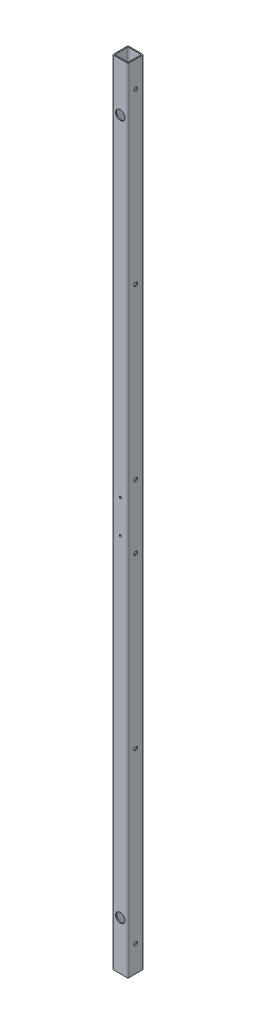
SolidWorks part; units mm, degrees
ref_plane "Front Plane" through (0, 0, 0) normal (0, 0, 1) x (1, 0, 0)
ref_plane "Top Plane" through (0, 0, 0) normal (0, 1, 0) x (1, 0, 0)
ref_plane "Right Plane" through (0, 0, 0) normal (1, 0, 0) x (0, 0, -1)
sketch "Sketch1" plane through (0, 0, 0) normal (0, 1, 0) x (1, 0, 0)
  line L0 (11.049, -11.049) -> (11.049, 11.049)
  line L1 (-12.7, -12.7) -> (12.7, -12.7)
  line L2 (-12.7, -12.7) -> (-12.7, 12.7)
  line L3 (-12.7, 12.7) -> (12.7, 12.7)
  line L4 (12.7, -12.7) -> (12.7, 12.7)
  line L5 (-12.7, -12.7) -> (12.7, 12.7) construction
  line L6 (-12.7, 12.7) -> (12.7, -12.7) construction
  line L7 (-11.049, 11.049) -> (11.049, 11.049)
  line L8 (-11.049, -11.049) -> (-11.049, 11.049)
  line L9 (-11.049, -11.049) -> (11.049, -11.049)
  point P0 (0, 0)
  dimension "D1" = 25.4
  dimension "D2" = 1.651
extrude "Boss-Extrude1" add sketch "Sketch1" along normal blind 1309.624
fillet "Fillet1" radius 1.27 8 edges at (-12.7, 654.812, 12.7) (-12.7, 654.812, -12.7) (12.7, 654.812, -12.7) (12.7, 654.812, 12.7) (-11.049, 654.812, -11.049) (11.049, 654.812, 11.049) (11.049, 654.812, -11.049) (-11.049, 654.812, 11.049)
hole_wizard "#1 (0.228) Diameter Hole1" positions "Sketch2" profile "Sketch3" hole size "#1" standard "ANSI Inch" end condition through all
sketch "Sketch2" plane through (12.7, 0, 0) normal (1, 0, 0) x (0, 0, -1)
  line L0 (0, 1309.624) -> (0, 0) construction
  line L1 (-11.43, 1309.624) -> (11.43, 1309.624) construction
  line L2 (11.43, 0) -> (-11.43, 0) construction
  line L4 (-11.43, 0) -> (11.43, 0) construction
  point P8 (0, 1266.444)
  point P82 (0, 987.044)
  point P83 (0, 707.644)
  point P84 (0, 43.18)
  point P107 (0, 322.58)
  point P108 (0, 601.98)
  dimension "D1" = 43.18
  dimension "D3" = 43.18
  dimension "D5" = 322.58
  dimension "D6" = 707.644
  dimension "D2" = 3
  dimension "D4" = 3
sketch "Sketch3" plane through (12.7, 601.98, 0) normal (0, 1, 0) x (0, 0, -1)
  line L0 (0, 0) -> (0, 25.4)
  line L1 (0, 25.4) -> (2.8956, 25.4)
  line L2 (2.8956, 25.4) -> (2.8956, 0)
  line L5 (2.8956, 0) -> (0, 0)
  line L11 (0, -6.35) -> (0, 107.95) construction
  dimension "Thru Hole Dia." = 5.7912
  dimension "Thru Hole Depth" = 25.4
hole_wizard "#8-32 Tapped Hole1" positions "Sketch4" profile "Sketch5" tap size "#8-32" standard "ANSI Inch" end condition through all
sketch "Sketch4" plane through (0, 0, -12.7) normal (0, 0, -1) x (-1, 0, 0)
  line L0 (-11.43, 0) -> (11.43, 1309.624) construction
  line L2 (0, 654.812) -> (-11.43, 654.812) construction
  line L3 (-11.43, 1309.624) -> (-11.43, 0) construction
  line L5 (0, 654.812) -> (0, 842.9154) construction
  line L6 (0, 654.812) -> (0, 575.682) construction
  point P19 (0, 682.244)
  point P25 (0, 627.38)
  dimension "D1" = 27.432
  dimension "D2" = 27.432
sketch "Sketch5" plane through (0, 627.38, -12.7) normal (1, 0, 0) x (0, 1, 0)
  line L0 (0, 0) -> (0, 25.4)
  line L1 (0, 25.4) -> (1.7272, 25.4)
  line L2 (1.7272, 25.4) -> (1.7272, 0)
  line L5 (1.7272, 0) -> (0, 0)
  line L11 (0, -6.35) -> (0, 107.95) construction
  dimension "Thru Tap Drill Dia." = 3.4544
  dimension "Thru Tap Drill Depth" = 25.4
cosmetic thread "Hole Thread1" parameters "D2"=4.1656
cosmetic thread "Hole Thread2" parameters "D2"=4.1656
hole_wizard "39/64 (0.60938) Diameter Hole1" positions "Sketch8" profile "Sketch9" hole size "39/64" standard "ANSI Inch" end condition through all
sketch "Sketch8" plane through (0, 0, 12.7) normal (0, 0, 1) x (1, 0, 0)
  line L0 (-11.43, 1309.624) -> (11.43, 1309.624) construction
  line L1 (-11.43, 0) -> (11.43, 0) construction
  point P0 (0, 1229.36)
  point P5 (0, 80.264)
  dimension "D1" = 80.264
  dimension "D2" = 80.264
sketch "Sketch9" plane through (0, 1229.36, 12.7) normal (1, 0, 0) x (0, -1, 0)
  line L0 (0, 0) -> (0, 25.4)
  line L1 (0, 25.4) -> (7.7391, 25.4)
  line L2 (7.7391, 25.4) -> (7.7391, 0)
  line L5 (7.7391, 0) -> (0, 0)
  line L11 (0, -6.35) -> (0, 107.95) construction
  dimension "Thru Hole Dia." = 15.4783
  dimension "Thru Hole Depth" = 25.4
